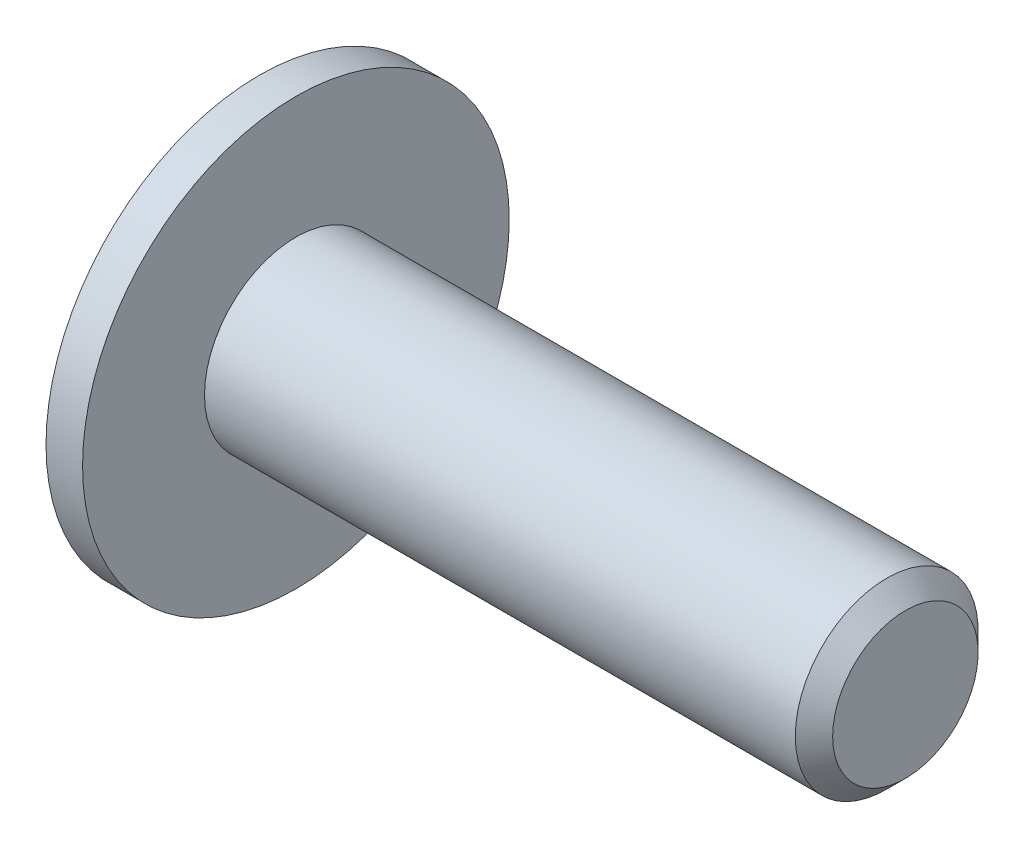
SolidWorks part; units mm, degrees
material "AISI 304"
ref_plane "正面" through (0, 0, 0) normal (0, 0, 1) x (1, 0, 0)
ref_plane "平面" through (0, 0, 0) normal (0, 1, 0) x (1, 0, 0)
ref_plane "右側面" through (0, 0, 0) normal (1, 0, 0) x (0, 0, -1)
ref_plane "Plane1" through (0, 0, 0) normal (0, 0, 1) x (1, 0, 0)
sketch "Sketch1" plane through (0, 0, 0) normal (0, 0, 1) x (1, 0, 0)
  line L0 (-1.65, 0) -> (-1.65, 1.95)
  line L1 (-0.6, 2.6) -> (-0.6, 3.5)
  line L2 (-0.6, 3.5) -> (0, 3.5)
  line L3 (0, 3.5) -> (0, 1.5)
  line L4 (0, 1.5) -> (9.6935, 1.5)
  line L5 (9.6935, 1.5) -> (10, 1.1935)
  line L6 (10, 1.1935) -> (10, 0)
  line L7 (10, 0) -> (-1.65, 0)
  line L8 (10, 0) -> (-1.65, 0) construction
  arc A0 (-1.65, 1.95) -> (-0.6, 2.6) centre (-0.2725, 0.8979) cw
revolve "Revolve1" add sketch "Sketch1" angle 360 about L8
cosmetic thread "Cosmetic Thread1"
ref_plane "Plane2" through (-1.65, 0, 0) normal (1, 0, 0) x (0, 0, -1)
sketch "Sketch2" plane through (-1.65, 0, 0) normal (1, 0, 0) x (0, 0, -1)
  line L0 (-1, -0.5774) -> (0, -1.1547)
  line L1 (0, -1.1547) -> (1, -0.5774)
  line L2 (1, -0.5774) -> (1, 0.5774)
  line L3 (1, 0.5774) -> (0, 1.1547)
  line L4 (0, 1.1547) -> (-1, 0.5774)
  line L5 (-1, 0.5774) -> (-1, -0.5774)
extrude "Cut-Extrude1" cut sketch "Sketch2" along normal blind 1.05
